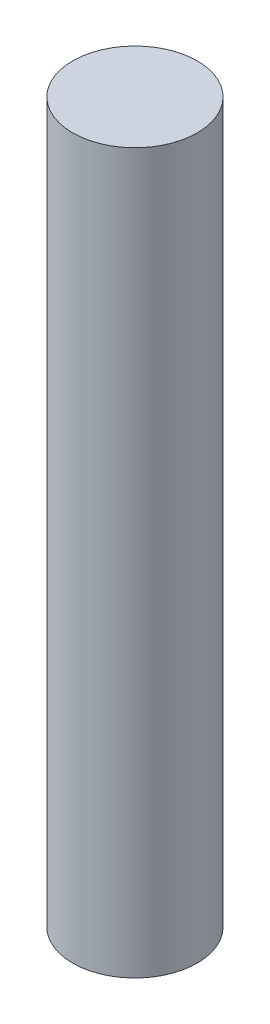
SolidWorks part; units mm, degrees
ref_plane "Front Plane" through (0, 0, 0) normal (0, 0, 1) x (1, 0, 0)
ref_plane "Top Plane" through (0, 0, 0) normal (0, 1, 0) x (1, 0, 0)
ref_plane "Right Plane" through (0, 0, 0) normal (1, 0, 0) x (0, 0, -1)
sketch "Sketch1" plane through (0, 0, 0) normal (0, 1, 0) x (1, 0, 0)
  circle A0 centre (0, 0) radius 3.302
  dimension "D1" = 6.604
extrude "Extrude1" add sketch "Sketch1" along normal blind 38.1
